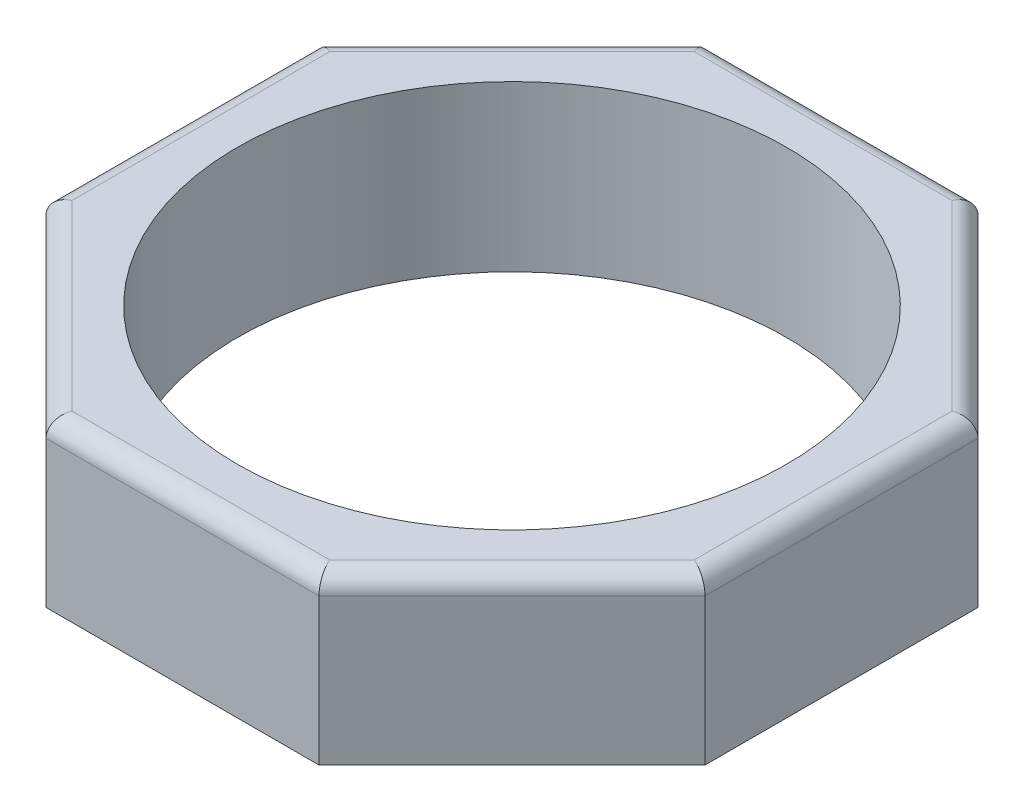
SolidWorks part; units mm, degrees
material "AISI 304"
ref_plane "Alzado" through (0, 0, 0) normal (0, 0, 1) x (1, 0, 0)
ref_plane "Planta" through (0, 0, 0) normal (0, 1, 0) x (1, 0, 0)
ref_plane "Vista lateral" through (0, 0, 0) normal (1, 0, 0) x (0, 0, -1)
sketch "Croquis1" plane through (0, 0, 0) normal (0, 1, 0) x (1, 0, 0)
  line L1 (18, 7.4558) -> (7.4558, 18)
  line L2 (7.4558, 18) -> (-7.4558, 18)
  line L3 (-7.4558, 18) -> (-18, 7.4558)
  line L4 (-18, 7.4558) -> (-18, -7.4558)
  line L5 (-18, -7.4558) -> (-7.4558, -18)
  line L6 (-7.4558, -18) -> (7.4558, -18)
  line L7 (7.4558, -18) -> (18, -7.4558)
  line L8 (18, -7.4558) -> (18, 7.4558)
  circle A0 centre (0, 0) radius 18 construction
  dimension "D1" = 36
extrude "Saliente-Extruir1" add sketch "Croquis1" along normal blind 9
sketch "Croquis2" plane through (0, 9, 0) normal (0, 1, 0) x (1, 0, 0)
  circle A0 centre (0, 0) radius 15
  dimension "D1" = 30
extrude "Cortar-Extruir1" cut sketch "Croquis2" against normal through all
fillet "Redondeo1" radius 1 8 edges at (-12.7279, 9, -12.7279) (0, 9, -18) (12.7279, 9, -12.7279) (18, 9, 0) (12.7279, 9, 12.7279) (0, 9, 18) (-12.7279, 9, 12.7279) (-18, 9, 0)
